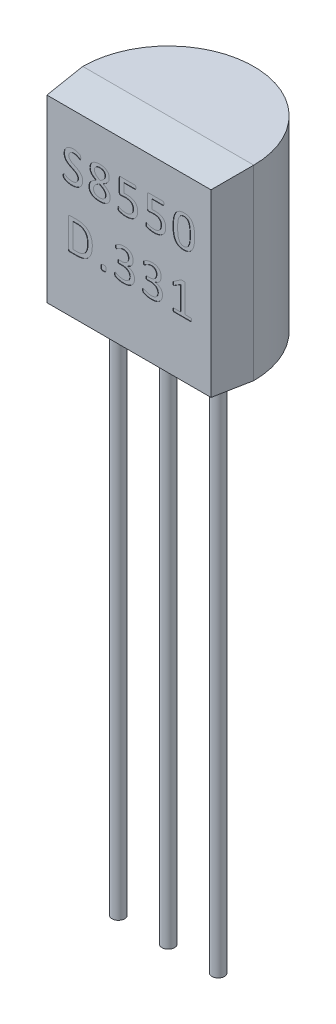
SolidWorks part; units mm, degrees
material "6061-T6 (SS)"
ref_plane "Front Plane" through (0, 0, 0) normal (0, 0, 1) x (1, 0, 0)
ref_plane "Top Plane" through (0, 0, 0) normal (0, 1, 0) x (1, 0, 0)
ref_plane "Right Plane" through (0, 0, 0) normal (1, 0, 0) x (0, 0, -1)
sketch "Sketch1" plane through (0, 0, 0) normal (0, 1, 0) x (1, 0, 0)
  line L0 (-2.175, 0) -> (2.175, 0)
  line L4 (0, 0) -> (0, -1.075) construction
  line L5 (0, 0) -> (0, 2.175) construction
  arc A0 (2.175, 0) -> (-2.175, 0) centre (0, 0) ccw
  dimension "D1" = 4.35
extrude "Boss-Extrude1" add sketch "Sketch1" along normal blind 4.75
sketch "Sketch2" plane through (0, 0, 0) normal (0, 0, 1) x (1, 0, 0)
  line L4 (-2.175, 0) -> (2.175, 0)
  line L5 (2.175, 0) -> (2.175, 4.75)
  line L6 (2.175, 4.75) -> (-2.175, 4.75)
  line L7 (-2.175, 4.75) -> (-2.175, 0)
  line L8 (-2.175, 0) -> (2.175, 0)
  line L9 (2.175, 0) -> (2.175, 4.75)
  line L10 (2.175, 4.75) -> (-2.175, 4.75)
  line L11 (-2.175, 4.75) -> (-2.175, 0)
  dimension "D1" = 0
extrude "Boss-Extrude2" add sketch "Sketch2" along normal blind 1 draft 5
sketch "Sketch3" plane through (0, 0, 1) normal (0, 0, 1) x (1, 0, 0)
  line L0 (0, 0) -> (0, 1.5) construction
  line L1 (0, 1.5) -> (0, 3) construction
  line L2 (-2.0875, 1.5) -> (2.0875, 1.5) construction
  line L3 (-2.0875, 4.6625) -> (-2.0875, 0.0875) construction
  line L4 (-2.0875, 3) -> (2.0875, 3) construction
  text T0 "S8550" font "Calibri" height 0.8
  text T1 "D.331" font "Calibri" height 0.8
  point P6 (-2.0875, 2.9145)
  dimension "D1" = 1.5
  dimension "D2" = 3
extrude "Cut-Extrude1" cut sketch "Sketch3" against normal blind 0.01
sketch "Sketch4" plane through (0, 0, 0) normal (0, -1, 0) x (1, 0, 0)
  line L0 (-1.27, 0) -> (1.27, 0) construction
  circle A0 centre (0, 0) radius 0.16
  circle A1 centre (1.27, 0) radius 0.16
  circle A2 centre (-1.27, 0) radius 0.16
  dimension "D2" = 0.32
  dimension "D1" = 2.54
extrude "Boss-Extrude3" add sketch "Sketch4" along normal blind 13.5 and the other way blind 1 separate body
